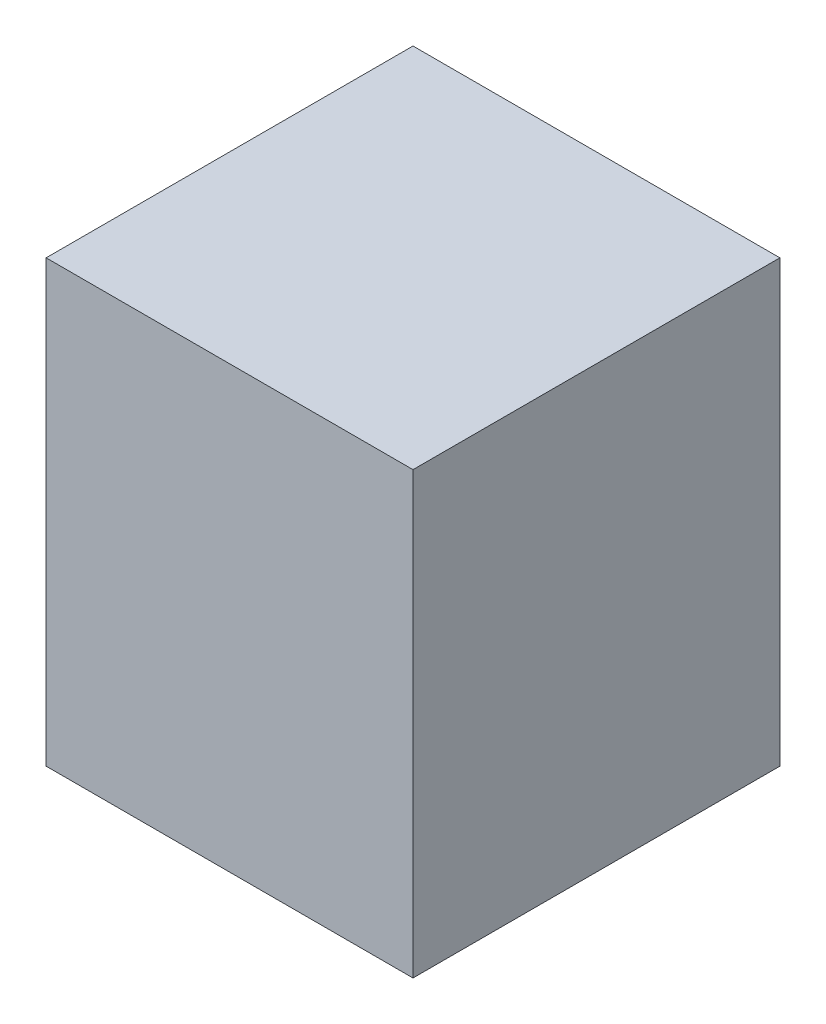
SolidWorks part; units mm, degrees
ref_plane "Front Plane" through (0, 0, 0) normal (0, 0, 1) x (1, 0, 0)
ref_plane "Top Plane" through (0, 0, 0) normal (0, 1, 0) x (1, 0, 0)
ref_plane "Right Plane" through (0, 0, 0) normal (1, 0, 0) x (0, 0, -1)
sketch "Sketch1" plane through (0, 0, 0) normal (0, 1, 0) x (1, 0, 0)
  line L1 (-25, 25) -> (25, 25)
  line L2 (-25, 25) -> (-25, -25)
  line L3 (-25, -25) -> (25, -25)
  line L4 (25, 25) -> (25, -25)
  dimension "D1" = 25
  dimension "D2" = 25
  dimension "D3" = 25
  dimension "D4" = 25
extrude "Boss-Extrude1" add sketch "Sketch1" along normal mid plane 60
